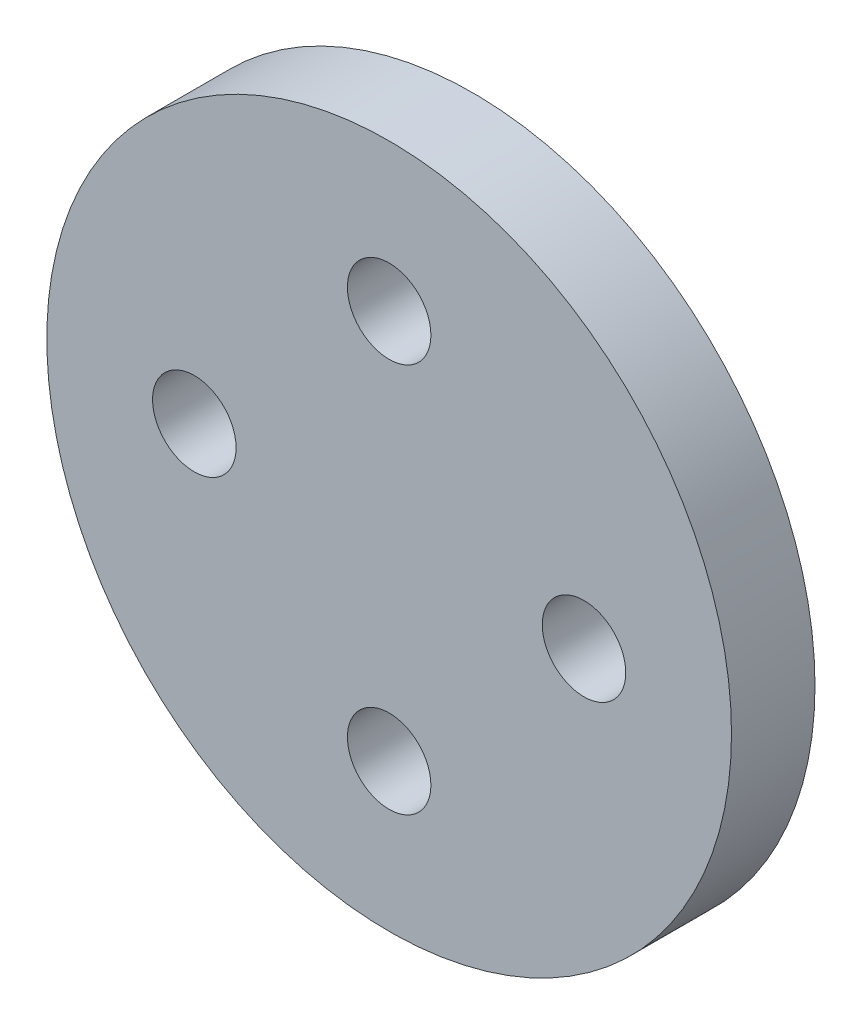
SolidWorks part; units mm, degrees
ref_plane "Front Plane" through (0, 0, 0) normal (0, 0, 1) x (1, 0, 0)
ref_plane "Top Plane" through (0, 0, 0) normal (0, 1, 0) x (1, 0, 0)
ref_plane "Right Plane" through (0, 0, 0) normal (1, 0, 0) x (0, 0, -1)
sketch "Sketch2" plane through (0, 0, 0) normal (0, 0, 1) x (1, 0, 0)
  circle A0 centre (0, 0) radius 12.3
  circle A5 centre (-7, 0) radius 1.5
  circle A6 centre (0, 7) radius 1.5
  circle A7 centre (7, 0) radius 1.5
  circle A8 centre (0, -7) radius 1.5
  dimension "D1" = 4
extrude "Boss-Extrude1" add sketch "Sketch2" along normal blind 3
sketch "Sketch3" plane through (0, 0, 0) normal (0, 0, -1) x (-1, 0, 0)
  circle A0 centre (0, 0) radius 3
extrude "Boss-Extrude2" add sketch "Sketch3" along normal blind 3
